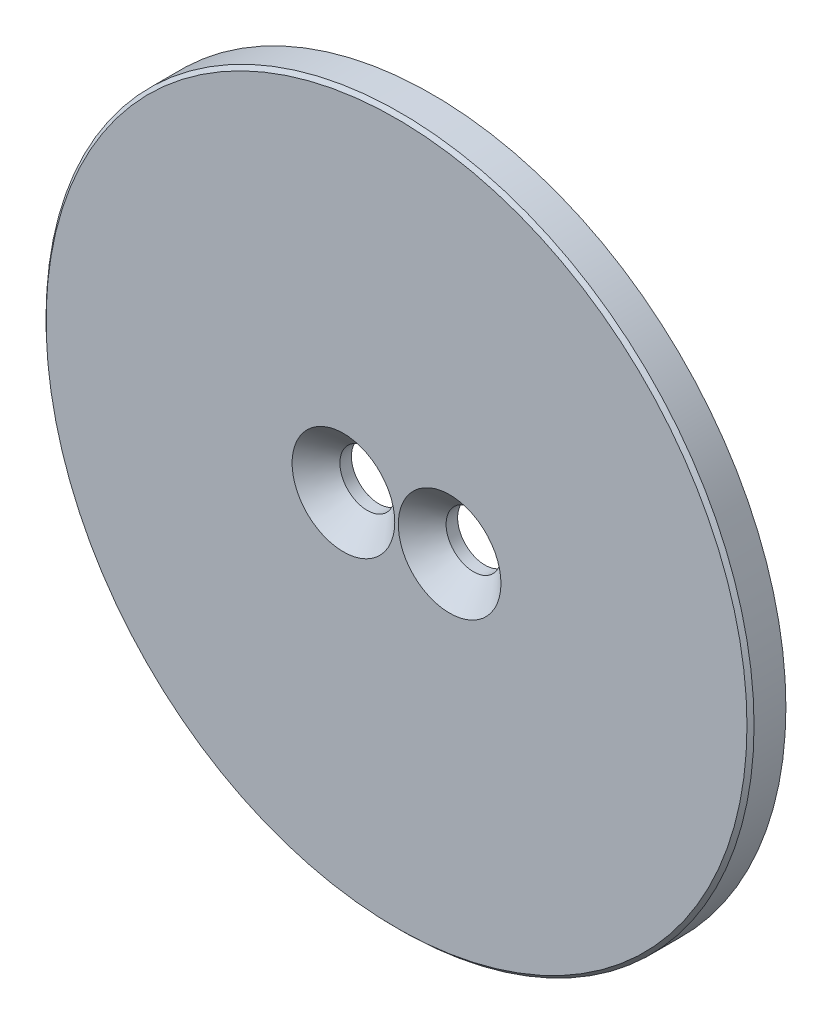
SolidWorks part; units mm, degrees
material "Thornel Mat VMA"
ref_plane "Front Plane" through (0, 0, 0) normal (0, 0, 1) x (1, 0, 0)
ref_plane "Top Plane" through (0, 0, 0) normal (0, 1, 0) x (1, 0, 0)
ref_plane "Right Plane" through (0, 0, 0) normal (1, 0, 0) x (0, 0, -1)
sketch "草图1" plane through (0, 0, 0) normal (0, 0, 1) x (1, 0, 0)
  circle A0 centre (0, 0) radius 20
  dimension "D1" = 40
extrude "凸台-拉伸1" add sketch "草图1" along normal blind 2
sketch "草图2" plane through (0, 0, 2) normal (0, 0, 1) x (1, 0, 0)
  line L0 (0, 0) -> (0, 10.8581) construction
  circle A0 centre (-3, 0) radius 1.55
  circle A1 centre (3, 0) radius 1.55
  dimension "D1" = 3.1
  dimension "D2" = 6
extrude "切除-拉伸1" cut sketch "草图2" against normal blind 2
hole_wizard "M3 六角凹锥坑螺钉的锥形沉头孔1" positions "3D草图1" profile "草图3" countersink size "M3" standard "ISO"
sketch3d "3D草图1"
  line L0 (-3, 0, 0) -> (-3, 0, 2) construction
  line L1 (3, 0, 0) -> (3, 0, 2) construction
  point P0 (-3, 0, 2)
  point P4 (3, 0, 2)
sketch "草图3" plane through (-3, 0, 2) normal (1, 0, 0) x (0, -1, 0)
  line L0 (0, 0) -> (0, 10)
  line L1 (0, 10) -> (1.55, 10)
  line L2 (1.55, 10) -> (1.55, 1.35)
  line L3 (1.55, 1.35) -> (2.9, 0)
  line L5 (2.9, 0) -> (0, 0)
  line L6 (-1.55, 1.35) -> (-2.9, 0) construction
  line L10 (0, 10) -> (-1.55, 10) construction
  line L11 (0, -6.35) -> (0, 107.95) construction
  dimension "孔直径" = 3.1
  dimension "孔深度" = 10
  dimension "近端锥形沉头孔直径" = 5.8
  dimension "近端锥形沉头孔角度" = 90
  dimension "导头角度" = 180
chamfer "倒角1" distance 0.2 angle 45 1 edges at (20, 0, 2)
